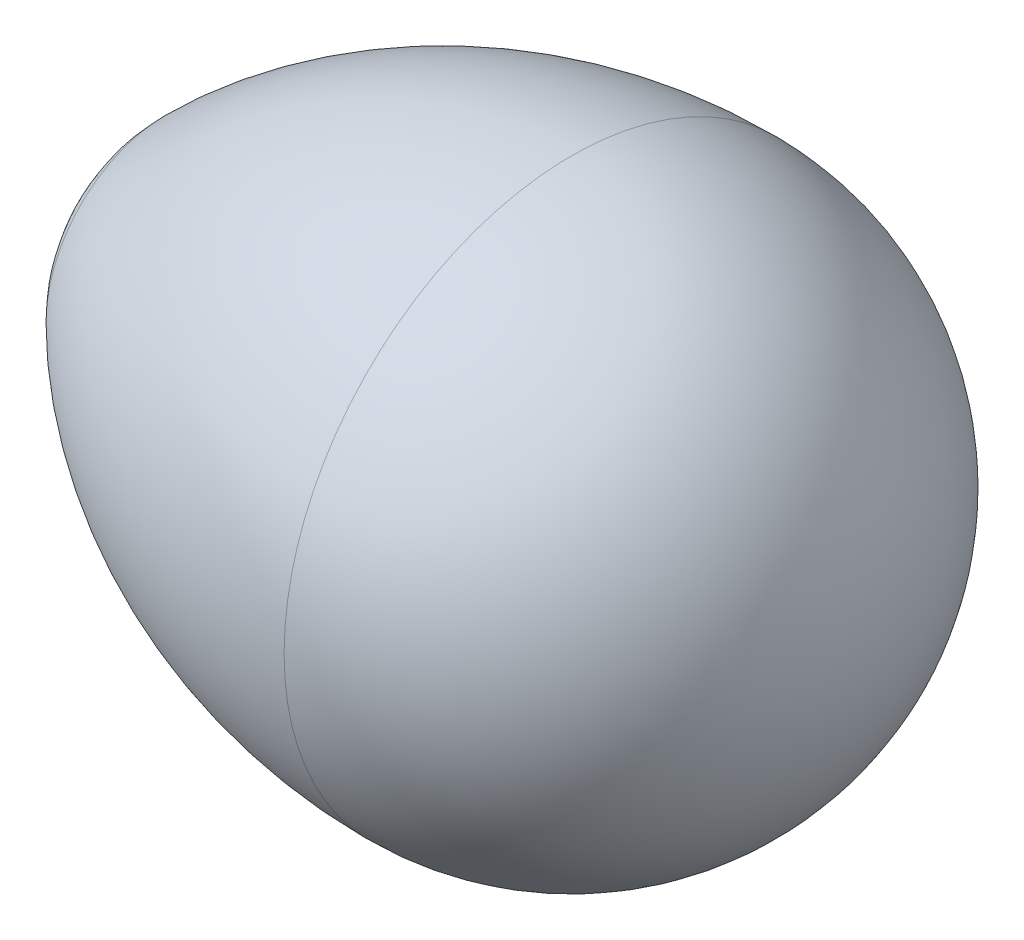
SolidWorks part; units mm, degrees
ref_plane "Plan de face" through (0, 0, 0) normal (0, 0, 1) x (1, 0, 0)
ref_plane "Plan de dessus" through (0, 0, 0) normal (0, 1, 0) x (1, 0, 0)
ref_plane "Plan de droite" through (0, 0, 0) normal (1, 0, 0) x (0, 0, -1)
sketch "Esquisse1" plane through (0, 0, 0) normal (0, 1, 0) x (1, 0, 0)
  line L0 (-28.4437, 0) -> (28.4437, 0) construction
  line L1 (0, -22) -> (0, 22) construction
  line L2 (-32.3223, 0) -> (0, 0) construction
  line L3 (-32.3223, 0) -> (0, 0)
  line L4 (-12.5, 12.5) -> (-12.5, -12.5) construction
  arc A0 (-32.3223, 0) -> (-30.1777, 5.1777) centre (-25, 0) cw
  arc A1 (0, 0) -> (-12.5, 12.5) centre (-12.5, 0) ccw
  arc A2 (-30.1777, 5.1777) -> (-12.5, 12.5) centre (-12.5, -12.5) cw
  point P2 (0, 0)
  point P11 (-12.5, 0)
revolve "Révolution1" add sketch "Esquisse1" angle 360 about L2
equation "\"D2@Esquisse1\"=(2*\"base@Esquisse1\")/(2+sqr(2 ))"
